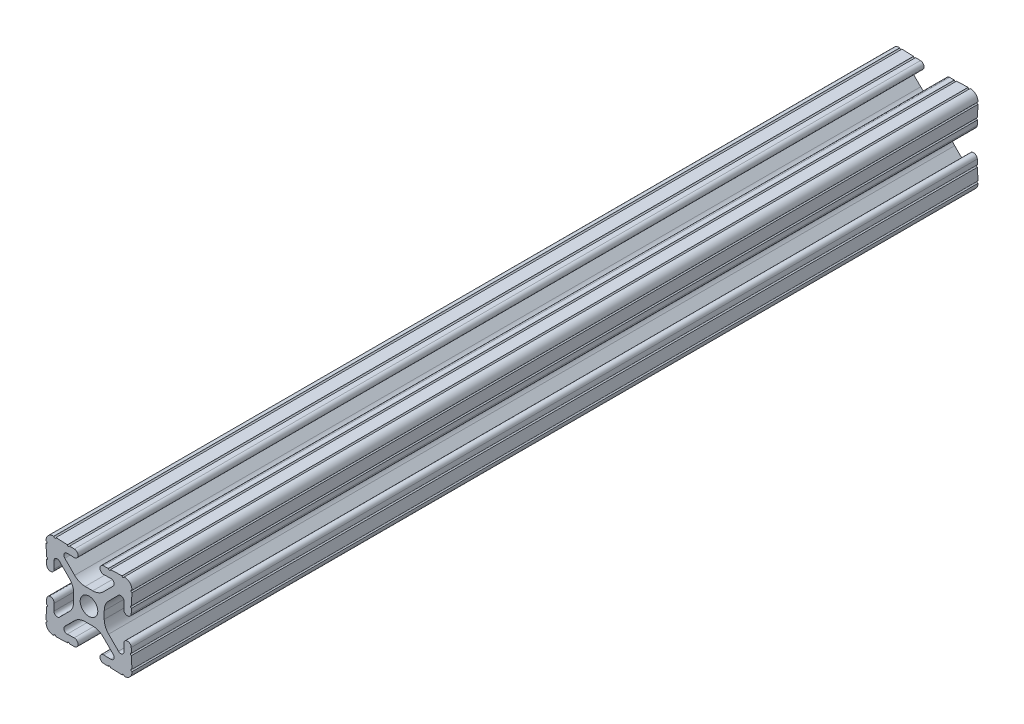
SolidWorks part; units mm, degrees
ref_plane "Front Plane" through (0, 0, 0) normal (0, 0, 1) x (1, 0, 0)
ref_plane "Top Plane" through (0, 0, 0) normal (0, 1, 0) x (1, 0, 0)
ref_plane "Right Plane" through (0, 0, 0) normal (1, 0, 0) x (0, 0, -1)
sketch "Sketch1" plane through (0, 0, 0) normal (0, 0, 1) x (1, 0, 0)
  line L0 (0, 12.7) -> (-12.7814, 12.7) construction
  line L1 (-4.5085, 0) -> (-4.5085, 2.9459)
  line L2 (-6.0437, 12.5461) -> (-10.0976, 12.6876) construction
  line L3 (-11.5616, 12.4229) -> (-4.3159, 12.1699) construction
  line L4 (-6.4364, 10.3486) -> (-6.3592, 12.5571) construction
  line L6 (-2.9459, 4.5085) -> (0, 4.5085)
  line L7 (0, 0) -> (0, 12.7) construction
  line L8 (0, 0) -> (-12.7814, 0) construction
  line L9 (0.7813, 0.7813) -> (-0.7813, -0.7813) construction
  line L10 (-2.9459, 4.5085) -> (-7.1484, 8.711)
  line L11 (-4.5085, 2.9459) -> (-8.711, 7.1484)
  line L13 (0, 0) -> (-12.7814, 12.7814) construction
  line L14 (-10.4131, 12.6987) -> (-4.3048, 12.4853)
  line L15 (-4.3048, 12.4853) -> (-4.382, 10.2769) construction
  line L16 (-4.382, 10.2769) -> (-6.4364, 10.3486)
  line L17 (-12.6987, 10.4131) -> (-12.4853, 4.3048)
  line L18 (-10.2769, 4.382) -> (-10.3486, 6.4364)
  circle A0 centre (0, 0) radius 2.6035
  arc A1 (-4.382, 10.2769) -> (-4.3048, 12.4853) centre (-4.3434, 11.3811) ccw
  arc A2 (-7.1484, 8.711) -> (-6.4364, 10.3486) centre (-6.4698, 9.3896) cw
  arc A3 (-8.711, 7.1484) -> (-10.3486, 6.4364) centre (-9.3896, 6.4698) ccw
  arc A4 (-10.2769, 4.382) -> (-12.4853, 4.3048) centre (-11.3811, 4.3434) cw
  arc A5 (-10.4131, 12.6987) -> (-12.6987, 10.4131) centre (-10.4902, 10.4902) ccw
  arc A6 (-10.4131, 12.6987) -> (-9.7821, 12.6766) centre (-10.0976, 12.6876) ccw
  arc A7 (-6.3592, 12.5571) -> (-5.7282, 12.5351) centre (-6.0437, 12.5461) ccw
  arc A8 (-12.5571, 6.3592) -> (-12.5351, 5.7282) centre (-12.5461, 6.0437) cw
  arc A9 (-12.6987, 10.4131) -> (-12.6766, 9.7821) centre (-12.6876, 10.0976) cw
  dimension "D1" = 5.207
  dimension "D5" = 14.859
  dimension "D9" = 2
  dimension "D2" = 25.4
  dimension "D12" = 0.6314
  dimension "D10" = 2.2098
  dimension "D3" = 9.017
  dimension "D4" = 9.017
  dimension "D6" = 25.4
  dimension "D7" = 6.477
  dimension "D8" = 2.2098
  dimension "D11" = 12.7
sketch "Sketch3" plane through (0, 0, 0) normal (0, 0, 1) x (1, 0, 0)
  line L0 (-2.9459, 4.5085) -> (0, 4.5085) construction
  line L1 (-2.9459, 4.5085) -> (-7.1484, 8.711) construction
  line L2 (-4.382, 10.2769) -> (-6.4364, 10.3486) construction
  line L3 (-10.4131, 12.6987) -> (-4.3048, 12.4853) construction
  line L4 (-4.5085, 0) -> (-4.5085, 2.9459) construction
  line L5 (-4.5085, 2.9459) -> (-8.711, 7.1484) construction
  line L6 (-10.2769, 4.382) -> (-10.3486, 6.4364) construction
  line L7 (-12.6987, 10.4131) -> (-12.4853, 4.3048) construction
  line L8 (-1.1153, 4.5085) -> (1.1153, 4.5085)
  line L9 (-4.2404, 5.803) -> (-7.1484, 8.711)
  line L10 (-4.382, 10.2769) -> (-6.4364, 10.3486)
  line L11 (-9.7821, 12.6766) -> (-6.3592, 12.5571)
  line L12 (-4.5085, -1.1153) -> (-4.5085, 1.1153)
  line L13 (-5.803, 4.2404) -> (-8.711, 7.1484)
  line L14 (-10.2769, 4.382) -> (-10.3486, 6.4364)
  line L15 (-12.6766, 9.7821) -> (-12.5571, 6.3592)
  line L16 (-5.7282, 12.5351) -> (-4.3048, 12.4853)
  line L17 (-12.5351, 5.7282) -> (-12.4853, 4.3048)
  line L18 (0, 0) -> (0, 12.7) construction
  line L19 (0, 0) -> (-12.7814, 0) construction
  line L20 (12.5351, 5.7282) -> (12.4853, 4.3048)
  line L21 (5.7282, 12.5351) -> (4.3048, 12.4853)
  line L22 (12.6766, 9.7821) -> (12.5571, 6.3592)
  line L23 (10.2769, 4.382) -> (10.3486, 6.4364)
  line L24 (5.803, 4.2404) -> (8.711, 7.1484)
  line L25 (4.5085, -1.1153) -> (4.5085, 1.1153)
  line L26 (9.7821, 12.6766) -> (6.3592, 12.5571)
  line L27 (4.382, 10.2769) -> (6.4364, 10.3486)
  line L28 (4.2404, 5.803) -> (7.1484, 8.711)
  line L29 (4.2404, -5.803) -> (7.1484, -8.711)
  line L30 (4.382, -10.2769) -> (6.4364, -10.3486)
  line L31 (9.7821, -12.6766) -> (6.3592, -12.5571)
  line L32 (5.803, -4.2404) -> (8.711, -7.1484)
  line L33 (10.2769, -4.382) -> (10.3486, -6.4364)
  line L34 (12.6766, -9.7821) -> (12.5571, -6.3592)
  line L35 (5.7282, -12.5351) -> (4.3048, -12.4853)
  line L36 (12.5351, -5.7282) -> (12.4853, -4.3048)
  line L37 (-12.5351, -5.7282) -> (-12.4853, -4.3048)
  line L38 (-5.7282, -12.5351) -> (-4.3048, -12.4853)
  line L39 (-12.6766, -9.7821) -> (-12.5571, -6.3592)
  line L40 (-10.2769, -4.382) -> (-10.3486, -6.4364)
  line L41 (-5.803, -4.2404) -> (-8.711, -7.1484)
  line L42 (-9.7821, -12.6766) -> (-6.3592, -12.5571)
  line L43 (-4.382, -10.2769) -> (-6.4364, -10.3486)
  line L44 (-4.2404, -5.803) -> (-7.1484, -8.711)
  line L45 (-1.1153, -4.5085) -> (1.1153, -4.5085)
  arc A0 (-10.4131, 12.6987) -> (-9.7821, 12.6766) centre (-10.0976, 12.6876) ccw construction
  arc A1 (-6.4364, 10.3486) -> (-7.1484, 8.711) centre (-6.4698, 9.3896) ccw construction
  arc A2 (-4.382, 10.2769) -> (-4.3048, 12.4853) centre (-4.3434, 11.3811) ccw construction
  arc A3 (-8.711, 7.1484) -> (-10.3486, 6.4364) centre (-9.3896, 6.4698) ccw construction
  arc A4 (-12.4853, 4.3048) -> (-10.2769, 4.382) centre (-11.3811, 4.3434) ccw construction
  arc A5 (-6.3592, 12.5571) -> (-5.7282, 12.5351) centre (-6.0437, 12.5461) ccw construction
  arc A6 (-10.4131, 12.6987) -> (-12.6987, 10.4131) centre (-10.4902, 10.4902) ccw construction
  arc A7 (-12.6766, 9.7821) -> (-12.6987, 10.4131) centre (-12.6876, 10.0976) ccw construction
  arc A8 (-12.5351, 5.7282) -> (-12.5571, 6.3592) centre (-12.5461, 6.0437) ccw construction
  arc A9 (-10.4131, 12.6987) -> (-9.7821, 12.6766) centre (-10.0976, 12.6876) ccw
  arc A10 (-6.4364, 10.3486) -> (-7.1484, 8.711) centre (-6.4698, 9.3896) ccw
  arc A11 (-4.382, 10.2769) -> (-4.3048, 12.4853) centre (-4.3434, 11.3811) ccw
  arc A12 (-8.711, 7.1484) -> (-10.3486, 6.4364) centre (-9.3896, 6.4698) ccw
  arc A13 (-12.4853, 4.3048) -> (-10.2769, 4.382) centre (-11.3811, 4.3434) ccw
  arc A14 (-6.3592, 12.5571) -> (-5.7282, 12.5351) centre (-6.0437, 12.5461) ccw
  arc A15 (-10.4131, 12.6987) -> (-12.6987, 10.4131) centre (-10.4902, 10.4902) ccw
  arc A16 (-12.6766, 9.7821) -> (-12.6987, 10.4131) centre (-12.6876, 10.0976) ccw
  arc A17 (-12.5351, 5.7282) -> (-12.5571, 6.3592) centre (-12.5461, 6.0437) ccw
  arc A18 (-1.1153, 4.5085) -> (-4.2404, 5.803) centre (-1.1153, 8.9281) cw
  arc A19 (4.5085, 1.1153) -> (5.803, 4.2404) centre (8.9281, 1.1153) cw
  arc A20 (1.1153, 4.5085) -> (4.2404, 5.803) centre (1.1153, 8.9281) ccw
  arc A21 (-4.5085, 1.1153) -> (-5.803, 4.2404) centre (-8.9281, 1.1153) ccw
  arc A22 (12.5351, 5.7282) -> (12.5571, 6.3592) centre (12.5461, 6.0437) cw
  arc A23 (12.6766, 9.7821) -> (12.6987, 10.4131) centre (12.6876, 10.0976) cw
  arc A24 (10.4131, 12.6987) -> (12.6987, 10.4131) centre (10.4902, 10.4902) cw
  arc A25 (6.3592, 12.5571) -> (5.7282, 12.5351) centre (6.0437, 12.5461) cw
  arc A26 (12.4853, 4.3048) -> (10.2769, 4.382) centre (11.3811, 4.3434) cw
  arc A27 (8.711, 7.1484) -> (10.3486, 6.4364) centre (9.3896, 6.4698) cw
  arc A28 (4.382, 10.2769) -> (4.3048, 12.4853) centre (4.3434, 11.3811) cw
  arc A29 (6.4364, 10.3486) -> (7.1484, 8.711) centre (6.4698, 9.3896) cw
  arc A30 (10.4131, 12.6987) -> (9.7821, 12.6766) centre (10.0976, 12.6876) cw
  arc A31 (10.4131, -12.6987) -> (9.7821, -12.6766) centre (10.0976, -12.6876) ccw
  arc A32 (6.4364, -10.3486) -> (7.1484, -8.711) centre (6.4698, -9.3896) ccw
  arc A33 (4.382, -10.2769) -> (4.3048, -12.4853) centre (4.3434, -11.3811) ccw
  arc A34 (8.711, -7.1484) -> (10.3486, -6.4364) centre (9.3896, -6.4698) ccw
  arc A35 (12.4853, -4.3048) -> (10.2769, -4.382) centre (11.3811, -4.3434) ccw
  arc A36 (6.3592, -12.5571) -> (5.7282, -12.5351) centre (6.0437, -12.5461) ccw
  arc A37 (10.4131, -12.6987) -> (12.6987, -10.4131) centre (10.4902, -10.4902) ccw
  arc A38 (12.6766, -9.7821) -> (12.6987, -10.4131) centre (12.6876, -10.0976) ccw
  arc A39 (12.5351, -5.7282) -> (12.5571, -6.3592) centre (12.5461, -6.0437) ccw
  arc A40 (-4.5085, -1.1153) -> (-5.803, -4.2404) centre (-8.9281, -1.1153) cw
  arc A41 (1.1153, -4.5085) -> (4.2404, -5.803) centre (1.1153, -8.9281) cw
  arc A42 (4.5085, -1.1153) -> (5.803, -4.2404) centre (8.9281, -1.1153) ccw
  arc A43 (-1.1153, -4.5085) -> (-4.2404, -5.803) centre (-1.1153, -8.9281) ccw
  arc A44 (-12.5351, -5.7282) -> (-12.5571, -6.3592) centre (-12.5461, -6.0437) cw
  arc A45 (-12.6766, -9.7821) -> (-12.6987, -10.4131) centre (-12.6876, -10.0976) cw
  arc A46 (-10.4131, -12.6987) -> (-12.6987, -10.4131) centre (-10.4902, -10.4902) cw
  arc A47 (-6.3592, -12.5571) -> (-5.7282, -12.5351) centre (-6.0437, -12.5461) cw
  arc A48 (-12.4853, -4.3048) -> (-10.2769, -4.382) centre (-11.3811, -4.3434) cw
  arc A49 (-8.711, -7.1484) -> (-10.3486, -6.4364) centre (-9.3896, -6.4698) cw
  arc A50 (-4.382, -10.2769) -> (-4.3048, -12.4853) centre (-4.3434, -11.3811) cw
  arc A51 (-6.4364, -10.3486) -> (-7.1484, -8.711) centre (-6.4698, -9.3896) cw
  arc A52 (-10.4131, -12.6987) -> (-9.7821, -12.6766) centre (-10.0976, -12.6876) cw
  circle A53 centre (0, 0) radius 2.6035 construction
  circle A54 centre (0, 0) radius 2.6035
  point P135 (4.5085, 0)
  dimension "D2" = 4.4196
extrude "Extrude1" add sketch "Sketch3" along normal mid plane 250
ref_plane "Plane1" through (12.4853, 4.3048, 125) normal (0.0349, 0.9994, 0) x (0.9994, -0.0349, 0)
equation "\"D10@Sketch1\" = \"D8@Sketch1\""
equation "\"D11@Sketch1\" = \"D6@Sketch1\"/2"
equation "\"D12@Sketch1\" = \"D8@Sketch1\"/3.5"
equation "\"D2@Sketch3\" = \"D8@Sketch1\"*2"
